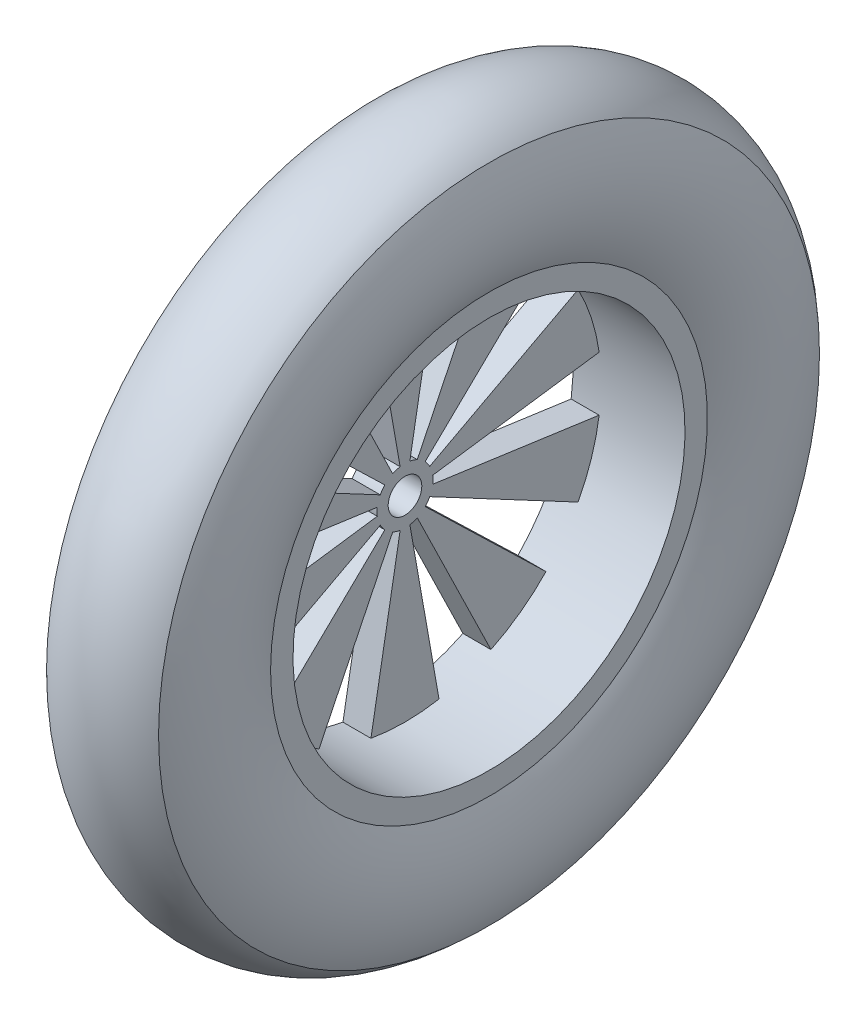
SolidWorks part; units mm, degrees
ref_plane "Front Plane" through (0, 0, 0) normal (0, 0, 1) x (1, 0, 0)
ref_plane "Top Plane" through (0, 0, 0) normal (0, 1, 0) x (1, 0, 0)
ref_plane "Right Plane" through (0, 0, 0) normal (1, 0, 0) x (0, 0, -1)
sketch "Sketch1" plane through (0, 0, 0) normal (0, 0, 1) x (1, 0, 0)
  line L0 (0, 0) -> (-35, 0) construction
  line L1 (-35, 0) -> (35, 0) construction
  line L2 (18, 78) -> (20, 78)
  line L3 (0, 70) -> (20, 70)
  line L4 (20, 70) -> (20, 78)
  line L5 (0, 72) -> (18, 72)
  line L6 (18, 72) -> (18, 78)
  line L8 (-18, 78) -> (-20, 78)
  line L9 (-20, 70) -> (-20, 78)
  line L10 (-18, 72) -> (-18, 78)
  line L11 (0, 70) -> (-20, 70)
  line L12 (0, 72) -> (-18, 72)
  dimension "D1" = 2
revolve "Revolve1" add sketch "Sketch1" angle 360 about L0
sketch "Sketch2" plane through (0, 0, 0) normal (0, 0, 1) x (1, 0, 0)
  line L0 (-54.5736, 0) -> (50.0699, 0) construction
  line L1 (-20, 78) -> (20, 78)
  arc A0 (-20, 78) -> (-20, 118) centre (20.3113, 98) cw
  arc A1 (-20, 118) -> (20, 118) centre (0, 98) cw
  arc A2 (20, 118) -> (20, 78) centre (-20.3113, 98) cw
revolve "Revolve2" add sketch "Sketch2" angle 360 about L0
sketch "Sketch4" plane through (-20, 0, 0) normal (-1, 0, 0) x (0, 0, 1)
  line L0 (4.3837, 8.9879) -> (30.686, 62.9156)
  line L1 (1.7365, 9.8481) -> (12.1554, 68.9365)
  line L2 (-1.7365, 9.8481) -> (-12.1554, 68.9365)
  line L3 (7.1934, 6.9466) -> (50.3538, 48.6261)
  line L4 (8.8295, 4.6947) -> (61.8063, 32.863)
  line L5 (9.9027, 1.3917) -> (69.3188, 9.7421)
  line L6 (9.9027, -1.3917) -> (69.3188, -9.7421)
  line L7 (8.8295, -4.6947) -> (61.8063, -32.863)
  line L8 (7.1934, -6.9466) -> (50.3538, -48.6261)
  line L9 (4.3837, -8.9879) -> (30.686, -62.9156)
  line L10 (1.7365, -9.8481) -> (12.1554, -68.9365)
  line L11 (-1.7365, -9.8481) -> (-12.1554, -68.9365)
  line L12 (-4.3837, -8.9879) -> (-30.686, -62.9156)
  line L13 (-7.1934, -6.9466) -> (-50.3538, -48.6261)
  line L14 (-8.8295, -4.6947) -> (-61.8063, -32.863)
  line L15 (-9.9027, -1.3917) -> (-69.3188, -9.7421)
  line L16 (-9.9027, 1.3917) -> (-69.3188, 9.7421)
  line L17 (-8.8295, 4.6947) -> (-61.8063, 32.863)
  line L18 (-7.1934, 6.9466) -> (-50.3538, 48.6261)
  line L19 (-4.3837, 8.9879) -> (-30.686, 62.9156)
  arc A1 (-1.7365, 9.8481) -> (-4.3837, 8.9879) centre (0, 0) ccw
  arc A2 (-12.1554, 68.9365) -> (12.1554, 68.9365) centre (0, 0) cw
  arc A3 (30.686, 62.9156) -> (50.3538, 48.6261) centre (0, 0) cw
  arc A4 (61.8063, 32.863) -> (69.3188, 9.7421) centre (0, 0) cw
  arc A5 (69.3188, -9.7421) -> (61.8063, -32.863) centre (0, 0) cw
  arc A6 (50.3538, -48.6261) -> (30.686, -62.9156) centre (0, 0) cw
  arc A7 (12.1554, -68.9365) -> (-12.1554, -68.9365) centre (0, 0) cw
  arc A8 (-30.686, -62.9156) -> (-50.3538, -48.6261) centre (0, 0) cw
  arc A9 (-61.8063, -32.863) -> (-69.3188, -9.7421) centre (0, 0) cw
  arc A10 (-69.3188, 9.7421) -> (-61.8063, 32.863) centre (0, 0) cw
  arc A11 (-50.3538, 48.6261) -> (-30.686, 62.9156) centre (0, 0) cw
  circle A12 centre (0, 0) radius 6
  arc A13 (4.3837, 8.9879) -> (1.7365, 9.8481) centre (0, 0) ccw
  arc A14 (8.8295, 4.6947) -> (7.1934, 6.9466) centre (0, 0) ccw
  arc A15 (9.9027, -1.3917) -> (9.9027, 1.3917) centre (0, 0) ccw
  arc A16 (7.1934, -6.9466) -> (8.8295, -4.6947) centre (0, 0) ccw
  arc A17 (1.7365, -9.8481) -> (4.3837, -8.9879) centre (0, 0) ccw
  arc A18 (-4.3837, -8.9879) -> (-1.7365, -9.8481) centre (0, 0) ccw
  arc A19 (-8.8295, -4.6947) -> (-7.1934, -6.9466) centre (0, 0) ccw
  arc A20 (-9.9027, 1.3917) -> (-9.9027, -1.3917) centre (0, 0) ccw
  arc A21 (-7.1934, 6.9466) -> (-8.8295, 4.6947) centre (0, 0) ccw
  dimension "D1" = 10
extrude "Boss-Extrude2" add sketch "Sketch4" against normal blind 10
